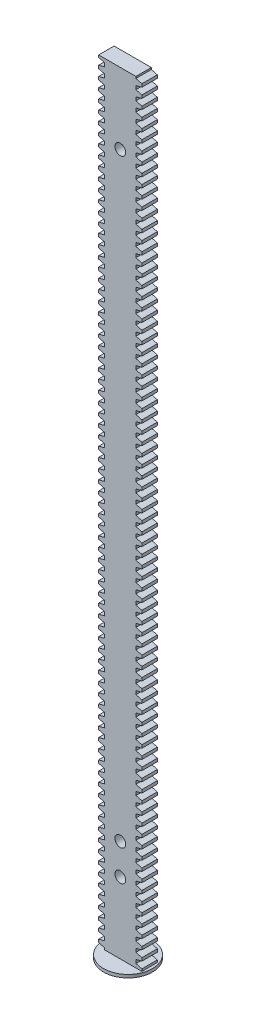
SolidWorks part; units mm, degrees
ref_plane "前视基准面" through (0, 0, 0) normal (0, 0, 1) x (1, 0, 0)
ref_plane "上视基准面" through (0, 0, 0) normal (0, 1, 0) x (1, 0, 0)
ref_plane "右视基准面" through (0, 0, 0) normal (1, 0, 0) x (0, 0, -1)
sketch "草图1" plane through (0, 0, 0) normal (0, 0, 1) x (1, 0, 0)
  line L0 (-85.9552, 233.5699) -> (-75.9552, 233.5699)
  line L1 (-86.008, 232.3319) -> (-86.008, 231.1796)
  line L2 (-86.008, 231.1796) -> (-87.9552, 230.676)
  line L3 (-87.9552, 230.676) -> (-87.9552, 229.6939)
  line L4 (-87.9552, 229.6939) -> (-86.008, 229.1903)
  line L5 (-86.008, 229.1903) -> (-86.008, 228.038)
  line L6 (-86.008, 228.038) -> (-87.9552, 227.5344)
  line L7 (-87.9552, 227.5344) -> (-87.9552, 226.5523)
  line L8 (-87.9552, 226.5523) -> (-86.008, 226.0487)
  line L9 (-86.008, 226.0487) -> (-86.008, 224.8964)
  line L10 (-86.008, 224.8964) -> (-87.9552, 224.3928)
  line L11 (-87.9552, 224.3928) -> (-87.9552, 223.4107)
  line L12 (-87.9552, 223.4107) -> (-86.008, 222.9071)
  line L13 (-86.008, 222.9071) -> (-86.008, 221.7548)
  line L14 (-86.008, 221.7548) -> (-87.9552, 221.2513)
  line L15 (-87.9552, 221.2513) -> (-87.9552, 220.2691)
  line L16 (-87.9552, 220.2691) -> (-86.008, 219.7655)
  line L17 (-86.008, 219.7655) -> (-86.008, 218.6132)
  line L18 (-86.008, 218.6132) -> (-87.9552, 218.1097)
  line L19 (-87.9552, 218.1097) -> (-87.9552, 217.1275)
  line L20 (-87.9552, 217.1275) -> (-86.008, 216.6239)
  line L21 (-86.008, 216.6239) -> (-86.008, 215.4717)
  line L22 (-86.008, 215.4717) -> (-87.9552, 214.9681)
  line L23 (-87.9552, 214.9681) -> (-87.9552, 213.9859)
  line L24 (-87.9552, 213.9859) -> (-86.008, 213.4823)
  line L25 (-86.008, 213.4823) -> (-86.008, 212.3301)
  line L26 (-86.008, 212.3301) -> (-87.9552, 211.8265)
  line L27 (-87.9552, 211.8265) -> (-87.9552, 210.8443)
  line L28 (-87.9552, 210.8443) -> (-86.008, 210.3407)
  line L29 (-86.008, 210.3407) -> (-86.008, 209.1885)
  line L30 (-86.008, 209.1885) -> (-87.9552, 208.6849)
  line L31 (-87.9552, 208.6849) -> (-87.9552, 207.7027)
  line L32 (-87.9552, 207.7027) -> (-86.008, 207.1991)
  line L33 (-86.008, 207.1991) -> (-86.008, 206.0469)
  line L34 (-86.008, 206.0469) -> (-87.9552, 205.5433)
  line L35 (-87.9552, 205.5433) -> (-87.9552, 204.5611)
  line L36 (-87.9552, 204.5611) -> (-86.008, 204.0575)
  line L37 (-86.008, 204.0575) -> (-86.008, 202.9053)
  line L38 (-86.008, 202.9053) -> (-87.9552, 202.4017)
  line L39 (-87.9552, 202.4017) -> (-87.9552, 201.4195)
  line L40 (-87.9552, 201.4195) -> (-86.008, 200.9159)
  line L41 (-86.008, 200.9159) -> (-86.008, 199.7637)
  line L42 (-86.008, 199.7637) -> (-87.9552, 199.2601)
  line L43 (-87.9552, 199.2601) -> (-87.9552, 198.2779)
  line L44 (-87.9552, 198.2779) -> (-86.008, 197.7743)
  line L45 (-86.008, 197.7743) -> (-86.008, 196.6221)
  line L46 (-86.008, 196.6221) -> (-87.9552, 196.1185)
  line L47 (-87.9552, 196.1185) -> (-87.9552, 195.1363)
  line L48 (-87.9552, 195.1363) -> (-86.008, 194.6328)
  line L49 (-86.008, 194.6328) -> (-86.008, 193.4805)
  line L50 (-86.008, 193.4805) -> (-87.9552, 192.9769)
  line L51 (-87.9552, 192.9769) -> (-87.9552, 191.9947)
  line L52 (-87.9552, 191.9947) -> (-86.008, 191.4912)
  line L53 (-86.008, 191.4912) -> (-86.008, 190.3389)
  line L54 (-86.008, 190.3389) -> (-87.9552, 189.8353)
  line L55 (-87.9552, 189.8353) -> (-87.9552, 188.8531)
  line L56 (-87.9552, 188.8531) -> (-86.008, 188.3496)
  line L57 (-86.008, 188.3496) -> (-86.008, 187.1973)
  line L58 (-86.008, 187.1973) -> (-87.9552, 186.6937)
  line L59 (-87.9552, 186.6937) -> (-87.9552, 185.7116)
  line L60 (-87.9552, 185.7116) -> (-86.008, 185.208)
  line L61 (-86.008, 185.208) -> (-86.008, 184.0557)
  line L62 (-86.008, 184.0557) -> (-87.9552, 183.5521)
  line L63 (-87.9552, 183.5521) -> (-87.9552, 182.57)
  line L64 (-87.9552, 182.57) -> (-86.008, 182.0664)
  line L65 (-86.008, 182.0664) -> (-86.008, 180.9141)
  line L66 (-86.008, 180.9141) -> (-87.9552, 180.4106)
  line L67 (-87.9552, 180.4106) -> (-87.9552, 179.4284)
  line L68 (-87.9552, 179.4284) -> (-86.008, 178.9248)
  line L69 (-86.008, 178.9248) -> (-86.008, 177.7725)
  line L70 (-86.008, 177.7725) -> (-87.9552, 177.269)
  line L71 (-87.9552, 177.269) -> (-87.9552, 176.2868)
  line L72 (-87.9552, 176.2868) -> (-86.008, 175.7832)
  line L73 (-86.008, 175.7832) -> (-86.008, 174.6309)
  line L74 (-86.008, 174.6309) -> (-87.9552, 174.1274)
  line L75 (-87.9552, 174.1274) -> (-87.9552, 173.1452)
  line L76 (-87.9552, 173.1452) -> (-86.008, 172.6416)
  line L77 (-86.008, 172.6416) -> (-86.008, 171.4894)
  line L78 (-86.008, 171.4894) -> (-87.9552, 170.9858)
  line L79 (-87.9552, 170.9858) -> (-87.9552, 170.0036)
  line L80 (-87.9552, 170.0036) -> (-86.008, 169.5)
  line L81 (-86.008, 169.5) -> (-86.008, 168.3478)
  line L82 (-86.008, 168.3478) -> (-87.9552, 167.8442)
  line L83 (-87.9552, 167.8442) -> (-87.9552, 166.862)
  line L84 (-87.9552, 166.862) -> (-86.008, 166.3584)
  line L85 (-86.008, 166.3584) -> (-86.008, 165.2062)
  line L86 (-86.008, 165.2062) -> (-87.9552, 164.7026)
  line L87 (-87.9552, 164.7026) -> (-87.9552, 163.7204)
  line L88 (-87.9552, 163.7204) -> (-86.008, 163.2168)
  line L89 (-86.008, 163.2168) -> (-86.008, 162.0646)
  line L90 (-86.008, 162.0646) -> (-87.9552, 161.561)
  line L91 (-87.9552, 161.561) -> (-87.9552, 160.5788)
  line L92 (-87.9552, 160.5788) -> (-86.008, 160.0752)
  line L93 (-86.008, 160.0752) -> (-86.008, 158.923)
  line L94 (-86.008, 158.923) -> (-87.9552, 158.4194)
  line L95 (-87.9552, 158.4194) -> (-87.9552, 157.4372)
  line L96 (-87.9552, 157.4372) -> (-86.008, 156.9336)
  line L97 (-86.008, 156.9336) -> (-86.008, 155.7814)
  line L98 (-86.008, 155.7814) -> (-87.9552, 155.2778)
  line L99 (-87.9552, 155.2778) -> (-87.9552, 154.2956)
  line L100 (-87.9552, 154.2956) -> (-86.008, 153.7921)
  line L101 (-86.008, 153.7921) -> (-86.008, 152.6398)
  line L102 (-86.008, 152.6398) -> (-87.9552, 152.1362)
  line L103 (-87.9552, 152.1362) -> (-87.9552, 151.154)
  line L104 (-87.9552, 151.154) -> (-86.008, 150.6505)
  line L105 (-86.008, 150.6505) -> (-86.008, 149.4982)
  line L106 (-86.008, 149.4982) -> (-87.9552, 148.9946)
  line L107 (-87.9552, 148.9946) -> (-87.9552, 148.0124)
  line L108 (-87.9552, 148.0124) -> (-86.008, 147.5089)
  line L109 (-86.008, 147.5089) -> (-86.008, 146.3566)
  line L110 (-86.008, 146.3566) -> (-87.9552, 145.853)
  line L111 (-87.9552, 145.853) -> (-87.9552, 144.8709)
  line L112 (-87.9552, 144.8709) -> (-86.008, 144.3673)
  line L113 (-86.008, 144.3673) -> (-86.008, 143.215)
  line L114 (-86.008, 143.215) -> (-87.9552, 142.7114)
  line L115 (-87.9552, 142.7114) -> (-87.9552, 141.7293)
  line L116 (-87.9552, 141.7293) -> (-86.008, 141.2257)
  line L117 (-86.008, 141.2257) -> (-86.008, 140.0734)
  line L118 (-86.008, 140.0734) -> (-87.9552, 139.5698)
  line L119 (-87.9552, 139.5698) -> (-87.9552, 138.5877)
  line L120 (-87.9552, 138.5877) -> (-86.008, 138.0841)
  line L121 (-86.008, 138.0841) -> (-86.008, 136.9318)
  line L122 (-86.008, 136.9318) -> (-87.9552, 136.4283)
  line L123 (-87.9552, 136.4283) -> (-87.9552, 135.4461)
  line L124 (-87.9552, 135.4461) -> (-86.008, 134.9425)
  line L125 (-86.008, 134.9425) -> (-86.008, 133.7902)
  line L126 (-86.008, 133.7902) -> (-87.9552, 133.2867)
  line L127 (-87.9552, 133.2867) -> (-87.9552, 132.3045)
  line L128 (-87.9552, 132.3045) -> (-86.008, 131.8009)
  line L129 (-86.008, 131.8009) -> (-86.008, 130.6486)
  line L130 (-86.008, 130.6486) -> (-87.9552, 130.1451)
  line L131 (-87.9552, 130.1451) -> (-87.9552, 129.1629)
  line L132 (-87.9552, 129.1629) -> (-86.008, 128.6593)
  line L133 (-86.008, 128.6593) -> (-86.008, 127.5071)
  line L134 (-86.008, 127.5071) -> (-87.9552, 127.0035)
  line L135 (-87.9552, 127.0035) -> (-87.9552, 126.0213)
  line L136 (-87.9552, 126.0213) -> (-86.008, 125.5177)
  line L137 (-86.008, 125.5177) -> (-86.008, 124.3655)
  line L138 (-86.008, 124.3655) -> (-87.9552, 123.8619)
  line L139 (-87.9552, 123.8619) -> (-87.9552, 122.8797)
  line L140 (-87.9552, 122.8797) -> (-86.008, 122.3761)
  line L141 (-86.008, 122.3761) -> (-86.008, 121.2239)
  line L142 (-86.008, 121.2239) -> (-87.9552, 120.7203)
  line L143 (-87.9552, 120.7203) -> (-87.9552, 119.7381)
  line L144 (-87.9552, 119.7381) -> (-86.008, 119.2345)
  line L145 (-86.008, 119.2345) -> (-86.008, 118.0823)
  line L146 (-86.008, 118.0823) -> (-87.9552, 117.5787)
  line L147 (-87.9552, 117.5787) -> (-87.9552, 116.5965)
  line L148 (-87.9552, 116.5965) -> (-86.008, 116.0929)
  line L149 (-86.008, 116.0929) -> (-86.008, 114.9407)
  line L150 (-86.008, 114.9407) -> (-87.9552, 114.4371)
  line L151 (-87.9552, 114.4371) -> (-87.9552, 113.4549)
  line L152 (-87.9552, 113.4549) -> (-86.008, 112.9513)
  line L153 (-86.008, 112.9513) -> (-86.008, 111.7991)
  line L154 (-86.008, 111.7991) -> (-87.9552, 111.2955)
  line L155 (-87.9552, 111.2955) -> (-87.9552, 110.3133)
  line L156 (-87.9552, 110.3133) -> (-86.008, 109.8098)
  line L157 (-86.008, 109.8098) -> (-86.008, 108.6575)
  line L158 (-86.008, 108.6575) -> (-87.9552, 108.1539)
  line L159 (-87.9552, 108.1539) -> (-87.9552, 107.1717)
  line L160 (-87.9552, 107.1717) -> (-86.008, 106.6682)
  line L161 (-86.008, 106.6682) -> (-86.008, 105.5159)
  line L162 (-86.008, 105.5159) -> (-87.9552, 105.0123)
  line L163 (-87.9552, 105.0123) -> (-87.9552, 104.0301)
  line L164 (-87.9552, 104.0301) -> (-86.008, 103.5266)
  line L165 (-86.008, 103.5266) -> (-86.008, 102.3743)
  line L166 (-86.008, 102.3743) -> (-87.9552, 101.8707)
  line L167 (-87.9552, 101.8707) -> (-87.9552, 100.8886)
  line L168 (-87.9552, 100.8886) -> (-86.008, 100.385)
  line L169 (-86.008, 100.385) -> (-86.008, 99.2327)
  line L170 (-86.008, 99.2327) -> (-87.9552, 98.7291)
  line L171 (-87.9552, 98.7291) -> (-87.9552, 97.747)
  line L172 (-87.9552, 97.747) -> (-86.008, 97.2434)
  line L173 (-86.008, 97.2434) -> (-86.008, 96.0911)
  line L174 (-86.008, 96.0911) -> (-87.9552, 95.5876)
  line L175 (-87.9552, 95.5876) -> (-87.9552, 94.6054)
  line L176 (-87.9552, 94.6054) -> (-86.008, 94.1018)
  line L177 (-86.008, 94.1018) -> (-86.008, 92.9495)
  line L178 (-86.008, 92.9495) -> (-87.9552, 92.446)
  line L179 (-87.9552, 92.446) -> (-87.9552, 91.4638)
  line L180 (-87.9552, 91.4638) -> (-86.008, 90.9602)
  line L181 (-86.008, 90.9602) -> (-86.008, 89.8079)
  line L182 (-86.008, 89.8079) -> (-87.9552, 89.3044)
  line L183 (-87.9552, 89.3044) -> (-87.9552, 88.3222)
  line L184 (-87.9552, 88.3222) -> (-86.008, 87.8186)
  line L185 (-86.008, 87.8186) -> (-86.008, 86.6664)
  line L186 (-86.008, 86.6664) -> (-87.9552, 86.1628)
  line L187 (-87.9552, 86.1628) -> (-87.9552, 85.1806)
  line L188 (-87.9552, 85.1806) -> (-86.008, 84.677)
  line L189 (-86.008, 84.677) -> (-86.008, 83.5248)
  line L190 (-86.008, 83.5248) -> (-87.9552, 83.0212)
  line L191 (-87.9552, 83.0212) -> (-87.9552, 82.039)
  line L192 (-87.9552, 82.039) -> (-86.008, 81.5354)
  line L193 (-86.008, 81.5354) -> (-86.008, 80.3832)
  line L194 (-86.008, 80.3832) -> (-87.9552, 79.8796)
  line L195 (-87.9552, 79.8796) -> (-87.9552, 78.8974)
  line L196 (-87.9552, 78.8974) -> (-86.008, 78.3938)
  line L197 (-86.008, 78.3938) -> (-86.008, 77.2416)
  line L198 (-86.008, 77.2416) -> (-87.9552, 76.738)
  line L199 (-87.9552, 76.738) -> (-87.9552, 75.7558)
  line L200 (-87.9552, 75.7558) -> (-86.008, 75.2522)
  line L201 (-86.008, 75.2522) -> (-86.008, 74.1)
  line L202 (-86.008, 74.1) -> (-87.9552, 73.5964)
  line L203 (-87.9552, 73.5964) -> (-87.9552, 72.6142)
  line L204 (-87.9552, 72.6142) -> (-86.008, 72.1106)
  line L205 (-86.008, 72.1106) -> (-86.008, 70.9584)
  line L206 (-86.008, 70.9584) -> (-87.9552, 70.4548)
  line L207 (-87.9552, 70.4548) -> (-87.9552, 69.4726)
  line L208 (-87.9552, 69.4726) -> (-86.008, 68.969)
  line L209 (-86.008, 68.969) -> (-86.008, 67.8168)
  line L210 (-86.008, 67.8168) -> (-87.9552, 67.3132)
  line L211 (-87.9552, 67.3132) -> (-87.9552, 66.331)
  line L212 (-87.9552, 66.331) -> (-86.008, 65.8275)
  line L213 (-86.008, 65.8275) -> (-86.008, 64.6752)
  line L214 (-86.008, 64.6752) -> (-87.9552, 64.1716)
  line L215 (-87.9552, 64.1716) -> (-87.9552, 63.1894)
  line L216 (-87.9552, 63.1894) -> (-86.008, 62.6859)
  line L217 (-86.008, 62.6859) -> (-86.008, 61.5336)
  line L218 (-86.008, 61.5336) -> (-87.9552, 61.03)
  line L219 (-87.9552, 61.03) -> (-87.9552, 60.0479)
  line L220 (-87.9552, 60.0479) -> (-86.008, 59.5443)
  line L221 (-86.008, 59.5443) -> (-86.008, 58.392)
  line L222 (-86.008, 58.392) -> (-87.9552, 57.8884)
  line L223 (-87.9552, 57.8884) -> (-87.9552, 56.9063)
  line L224 (-87.9552, 56.9063) -> (-86.008, 56.4027)
  line L225 (-86.008, 56.4027) -> (-86.008, 55.2504)
  line L226 (-86.008, 55.2504) -> (-87.9552, 54.7468)
  line L227 (-87.9552, 54.7468) -> (-87.9552, 53.7647)
  line L228 (-87.9552, 53.7647) -> (-86.008, 53.2611)
  line L229 (-86.008, 53.2611) -> (-86.008, 52.1088)
  line L230 (-86.008, 52.1088) -> (-87.9552, 51.6053)
  line L231 (-87.9552, 51.6053) -> (-87.9552, 50.6231)
  line L232 (-87.9552, 50.6231) -> (-86.008, 50.1195)
  line L233 (-86.008, 50.1195) -> (-86.008, 48.9672)
  line L234 (-86.008, 48.9672) -> (-87.9552, 48.4637)
  line L235 (-87.9552, 48.4637) -> (-87.9552, 47.4815)
  line L236 (-87.9552, 47.4815) -> (-86.008, 46.9779)
  line L237 (-86.008, 46.9779) -> (-86.008, 45.8256)
  line L238 (-86.008, 45.8256) -> (-87.9552, 45.3221)
  line L239 (-87.9552, 45.3221) -> (-87.9552, 44.3399)
  line L240 (-87.9552, 44.3399) -> (-86.008, 43.8363)
  line L241 (-86.008, 43.8363) -> (-86.008, 42.6841)
  line L242 (-86.008, 42.6841) -> (-87.9552, 42.1805)
  line L243 (-87.9552, 42.1805) -> (-87.9552, 41.1983)
  line L244 (-87.9552, 41.1983) -> (-86.008, 40.6947)
  line L245 (-86.008, 40.6947) -> (-86.008, 39.5425)
  line L246 (-86.008, 39.5425) -> (-87.9552, 39.0389)
  line L247 (-87.9552, 39.0389) -> (-87.9552, 38.0567)
  line L248 (-87.9552, 38.0567) -> (-86.008, 37.5531)
  line L249 (-86.008, 37.5531) -> (-86.008, 36.4009)
  line L250 (-86.008, 36.4009) -> (-87.9552, 35.8973)
  line L251 (-87.9552, 35.8973) -> (-87.9552, 34.9151)
  line L252 (-87.9552, 34.9151) -> (-86.008, 34.4115)
  line L253 (-86.008, 34.4115) -> (-86.008, 33.2593)
  line L254 (-86.008, 33.2593) -> (-87.9552, 32.7557)
  line L255 (-87.9552, 32.7557) -> (-87.9552, 31.7735)
  line L256 (-87.9552, 31.7735) -> (-86.008, 31.2699)
  line L257 (-86.008, 31.2699) -> (-86.008, 30.1177)
  line L258 (-86.008, 30.1177) -> (-87.9552, 29.6141)
  line L259 (-87.9552, 29.6141) -> (-87.9552, 28.6319)
  line L260 (-87.9552, 28.6319) -> (-86.008, 28.1283)
  line L261 (-86.008, 28.1283) -> (-86.008, 26.9761)
  line L262 (-86.008, 26.9761) -> (-87.9552, 26.4725)
  line L263 (-87.9552, 26.4725) -> (-87.9552, 25.4903)
  line L264 (-87.9552, 25.4903) -> (-86.008, 24.9868)
  line L265 (-86.008, 24.9868) -> (-86.008, 23.8345)
  line L266 (-86.008, 23.8345) -> (-87.9552, 23.3309)
  line L267 (-87.9552, 23.3309) -> (-87.9552, 22.3487)
  line L268 (-87.9552, 22.3487) -> (-86.008, 21.8452)
  line L269 (-86.008, 21.8452) -> (-86.008, 20.6929)
  line L270 (-86.008, 20.6929) -> (-87.9552, 20.1893)
  line L271 (-87.9552, 20.1893) -> (-87.9552, 19.2071)
  line L272 (-87.9552, 19.2071) -> (-86.008, 18.7036)
  line L273 (-86.008, 18.7036) -> (-86.008, 17.5513)
  line L274 (-86.008, 17.5513) -> (-87.9552, 17.0477)
  line L275 (-87.9552, 17.0477) -> (-87.9552, 16.0656)
  line L276 (-87.9552, 16.0656) -> (-86.008, 15.562)
  line L277 (-86.008, 15.562) -> (-86.008, 14.4097)
  line L278 (-86.008, 14.4097) -> (-87.9552, 13.9061)
  line L279 (-87.9552, 13.9061) -> (-87.9552, 12.924)
  line L280 (-87.9552, 12.924) -> (-86.008, 12.4204)
  line L281 (-86.008, 12.4204) -> (-86.008, 11.2681)
  line L282 (-86.008, 11.2681) -> (-87.9552, 10.7645)
  line L283 (-87.9552, 10.7645) -> (-87.9552, 9.7824)
  line L284 (-87.9552, 9.7824) -> (-86.008, 9.2788)
  line L285 (-86.008, 9.2788) -> (-86.008, 8.1265)
  line L286 (-86.008, 8.1265) -> (-87.9552, 7.623)
  line L287 (-87.9552, 7.623) -> (-87.9552, 6.6408)
  line L288 (-87.9552, 6.6408) -> (-86.008, 6.1372)
  line L289 (-86.008, 6.1372) -> (-86.008, 4.9849)
  line L290 (-86.008, 4.9849) -> (-87.9552, 4.4814)
  line L291 (-87.9552, 4.4814) -> (-87.9552, 3.4992)
  line L292 (-87.9552, 3.4992) -> (-86.008, 2.9956)
  line L293 (-86.008, 2.9956) -> (-86.008, 1.8434)
  line L294 (-86.008, 1.8434) -> (-87.9552, 1.3398)
  line L295 (-87.9552, 1.3398) -> (-87.9552, 0.3576)
  line L296 (-87.9552, 0.3576) -> (-86.008, -0.146)
  line L297 (-86.008, -0.146) -> (-86.008, -1.2982)
  line L298 (-86.008, -1.2982) -> (-87.9552, -1.8018)
  line L299 (-87.9552, -1.8018) -> (-87.9552, -2.784)
  line L300 (-87.9552, -2.784) -> (-86.008, -3.2876)
  line L301 (-86.008, -3.2876) -> (-86.008, -4.4398)
  line L302 (-86.008, -4.4398) -> (-87.9552, -4.9434)
  line L303 (-87.9552, -4.9434) -> (-87.9552, -5.9256)
  line L304 (-87.9552, -5.9256) -> (-86.008, -6.4292)
  line L305 (-86.008, -6.4292) -> (-86.008, -7.5814)
  line L306 (-86.008, -7.5814) -> (-87.9552, -8.085)
  line L307 (-87.9552, -8.085) -> (-87.9552, -9.0672)
  line L308 (-87.9552, -9.0672) -> (-86.008, -9.5708)
  line L309 (-86.008, -9.5708) -> (-86.008, -10.723)
  line L310 (-86.008, -10.723) -> (-87.9552, -11.2266)
  line L311 (-87.9552, -11.2266) -> (-87.9552, -12.2088)
  line L312 (-87.9552, -12.2088) -> (-86.008, -12.7124)
  line L313 (-86.008, -12.7124) -> (-86.008, -13.8646)
  line L314 (-86.008, -13.8646) -> (-87.9552, -14.3682)
  line L315 (-87.9552, -14.3682) -> (-87.9552, -15.3504)
  line L316 (-87.9552, -15.3504) -> (-86.008, -15.854)
  line L317 (-86.008, -15.854) -> (-86.008, -16.4301)
  line L318 (-86.008, -16.4301) -> (-85.9552, -16.4301) construction
  line L319 (-85.9552, -16.4301) -> (-85.9552, 233.5699) construction
  line L320 (-85.9552, 233.5699) -> (-87.9552, 233.5699)
  line L321 (-87.9552, 233.5699) -> (-87.9552, 232.8354)
  line L322 (-87.9552, 232.8354) -> (-86.008, 232.3319)
  line L323 (-75.9552, 233.5699) -> (-75.9552, -16.4301) construction
  line L324 (-75.9552, -16.4301) -> (-86.008, -16.4301)
  line L325 (-75.9024, -15.192) -> (-75.9024, -14.0398)
  line L326 (-75.9024, -14.0398) -> (-73.9552, -13.5362)
  line L327 (-73.9552, -13.5362) -> (-73.9552, -12.554)
  line L328 (-73.9552, -12.554) -> (-75.9024, -12.0504)
  line L329 (-75.9024, -12.0504) -> (-75.9024, -10.8982)
  line L330 (-75.9024, -10.8982) -> (-73.9552, -10.3946)
  line L331 (-73.9552, -10.3946) -> (-73.9552, -9.4124)
  line L332 (-73.9552, -9.4124) -> (-75.9024, -8.9088)
  line L333 (-75.9024, -8.9088) -> (-75.9024, -7.7566)
  line L334 (-75.9024, -7.7566) -> (-73.9552, -7.253)
  line L335 (-73.9552, -7.253) -> (-73.9552, -6.2708)
  line L336 (-73.9552, -6.2708) -> (-75.9024, -5.7672)
  line L337 (-75.9024, -5.7672) -> (-75.9024, -4.615)
  line L338 (-75.9024, -4.615) -> (-73.9552, -4.1114)
  line L339 (-73.9552, -4.1114) -> (-73.9552, -3.1292)
  line L340 (-73.9552, -3.1292) -> (-75.9024, -2.6257)
  line L341 (-75.9024, -2.6257) -> (-75.9024, -1.4734)
  line L342 (-75.9024, -1.4734) -> (-73.9552, -0.9698)
  line L343 (-73.9552, -0.9698) -> (-73.9552, 0.0124)
  line L344 (-73.9552, 0.0124) -> (-75.9024, 0.5159)
  line L345 (-75.9024, 0.5159) -> (-75.9024, 1.6682)
  line L346 (-75.9024, 1.6682) -> (-73.9552, 2.1718)
  line L347 (-73.9552, 2.1718) -> (-73.9552, 3.154)
  line L348 (-73.9552, 3.154) -> (-75.9024, 3.6575)
  line L349 (-75.9024, 3.6575) -> (-75.9024, 4.8098)
  line L350 (-75.9024, 4.8098) -> (-73.9552, 5.3134)
  line L351 (-73.9552, 5.3134) -> (-73.9552, 6.2955)
  line L352 (-73.9552, 6.2955) -> (-75.9024, 6.7991)
  line L353 (-75.9024, 6.7991) -> (-75.9024, 7.9514)
  line L354 (-75.9024, 7.9514) -> (-73.9552, 8.455)
  line L355 (-73.9552, 8.455) -> (-73.9552, 9.4371)
  line L356 (-73.9552, 9.4371) -> (-75.9024, 9.9407)
  line L357 (-75.9024, 9.9407) -> (-75.9024, 11.093)
  line L358 (-75.9024, 11.093) -> (-73.9552, 11.5965)
  line L359 (-73.9552, 11.5965) -> (-73.9552, 12.5787)
  line L360 (-73.9552, 12.5787) -> (-75.9024, 13.0823)
  line L361 (-75.9024, 13.0823) -> (-75.9024, 14.2346)
  line L362 (-75.9024, 14.2346) -> (-73.9552, 14.7381)
  line L363 (-73.9552, 14.7381) -> (-73.9552, 15.7203)
  line L364 (-73.9552, 15.7203) -> (-75.9024, 16.2239)
  line L365 (-75.9024, 16.2239) -> (-75.9024, 17.3762)
  line L366 (-75.9024, 17.3762) -> (-73.9552, 17.8797)
  line L367 (-73.9552, 17.8797) -> (-73.9552, 18.8619)
  line L368 (-73.9552, 18.8619) -> (-75.9024, 19.3655)
  line L369 (-75.9024, 19.3655) -> (-75.9024, 20.5177)
  line L370 (-75.9024, 20.5177) -> (-73.9552, 21.0213)
  line L371 (-73.9552, 21.0213) -> (-73.9552, 22.0035)
  line L372 (-73.9552, 22.0035) -> (-75.9024, 22.5071)
  line L373 (-75.9024, 22.5071) -> (-75.9024, 23.6593)
  line L374 (-75.9024, 23.6593) -> (-73.9552, 24.1629)
  line L375 (-73.9552, 24.1629) -> (-73.9552, 25.1451)
  line L376 (-73.9552, 25.1451) -> (-75.9024, 25.6487)
  line L377 (-75.9024, 25.6487) -> (-75.9024, 26.8009)
  line L378 (-75.9024, 26.8009) -> (-73.9552, 27.3045)
  line L379 (-73.9552, 27.3045) -> (-73.9552, 28.2867)
  line L380 (-73.9552, 28.2867) -> (-75.9024, 28.7903)
  line L381 (-75.9024, 28.7903) -> (-75.9024, 29.9425)
  line L382 (-75.9024, 29.9425) -> (-73.9552, 30.4461)
  line L383 (-73.9552, 30.4461) -> (-73.9552, 31.4283)
  line L384 (-73.9552, 31.4283) -> (-75.9024, 31.9319)
  line L385 (-75.9024, 31.9319) -> (-75.9024, 33.0841)
  line L386 (-75.9024, 33.0841) -> (-73.9552, 33.5877)
  line L387 (-73.9552, 33.5877) -> (-73.9552, 34.5699)
  line L388 (-73.9552, 34.5699) -> (-75.9024, 35.0735)
  line L389 (-75.9024, 35.0735) -> (-75.9024, 36.2257)
  line L390 (-75.9024, 36.2257) -> (-73.9552, 36.7293)
  line L391 (-73.9552, 36.7293) -> (-73.9552, 37.7115)
  line L392 (-73.9552, 37.7115) -> (-75.9024, 38.2151)
  line L393 (-75.9024, 38.2151) -> (-75.9024, 39.3673)
  line L394 (-75.9024, 39.3673) -> (-73.9552, 39.8709)
  line L395 (-73.9552, 39.8709) -> (-73.9552, 40.8531)
  line L396 (-73.9552, 40.8531) -> (-75.9024, 41.3566)
  line L397 (-75.9024, 41.3566) -> (-75.9024, 42.5089)
  line L398 (-75.9024, 42.5089) -> (-73.9552, 43.0125)
  line L399 (-73.9552, 43.0125) -> (-73.9552, 43.9947)
  line L400 (-73.9552, 43.9947) -> (-75.9024, 44.4982)
  line L401 (-75.9024, 44.4982) -> (-75.9024, 45.6505)
  line L402 (-75.9024, 45.6505) -> (-73.9552, 46.1541)
  line L403 (-73.9552, 46.1541) -> (-73.9552, 47.1362)
  line L404 (-73.9552, 47.1362) -> (-75.9024, 47.6398)
  line L405 (-75.9024, 47.6398) -> (-75.9024, 48.7921)
  line L406 (-75.9024, 48.7921) -> (-73.9552, 49.2957)
  line L407 (-73.9552, 49.2957) -> (-73.9552, 50.2778)
  line L408 (-73.9552, 50.2778) -> (-75.9024, 50.7814)
  line L409 (-75.9024, 50.7814) -> (-75.9024, 51.9337)
  line L410 (-75.9024, 51.9337) -> (-73.9552, 52.4373)
  line L411 (-73.9552, 52.4373) -> (-73.9552, 53.4194)
  line L412 (-73.9552, 53.4194) -> (-75.9024, 53.923)
  line L413 (-75.9024, 53.923) -> (-75.9024, 55.0753)
  line L414 (-75.9024, 55.0753) -> (-73.9552, 55.5788)
  line L415 (-73.9552, 55.5788) -> (-73.9552, 56.561)
  line L416 (-73.9552, 56.561) -> (-75.9024, 57.0646)
  line L417 (-75.9024, 57.0646) -> (-75.9024, 58.2169)
  line L418 (-75.9024, 58.2169) -> (-73.9552, 58.7204)
  line L419 (-73.9552, 58.7204) -> (-73.9552, 59.7026)
  line L420 (-73.9552, 59.7026) -> (-75.9024, 60.2062)
  line L421 (-75.9024, 60.2062) -> (-75.9024, 61.3585)
  line L422 (-75.9024, 61.3585) -> (-73.9552, 61.862)
  line L423 (-73.9552, 61.862) -> (-73.9552, 62.8442)
  line L424 (-73.9552, 62.8442) -> (-75.9024, 63.3478)
  line L425 (-75.9024, 63.3478) -> (-75.9024, 64.5)
  line L426 (-75.9024, 64.5) -> (-73.9552, 65.0036)
  line L427 (-73.9552, 65.0036) -> (-73.9552, 65.9858)
  line L428 (-73.9552, 65.9858) -> (-75.9024, 66.4894)
  line L429 (-75.9024, 66.4894) -> (-75.9024, 67.6416)
  line L430 (-75.9024, 67.6416) -> (-73.9552, 68.1452)
  line L431 (-73.9552, 68.1452) -> (-73.9552, 69.1274)
  line L432 (-73.9552, 69.1274) -> (-75.9024, 69.631)
  line L433 (-75.9024, 69.631) -> (-75.9024, 70.7832)
  line L434 (-75.9024, 70.7832) -> (-73.9552, 71.2868)
  line L435 (-73.9552, 71.2868) -> (-73.9552, 72.269)
  line L436 (-73.9552, 72.269) -> (-75.9024, 72.7726)
  line L437 (-75.9024, 72.7726) -> (-75.9024, 73.9248)
  line L438 (-75.9024, 73.9248) -> (-73.9552, 74.4284)
  line L439 (-73.9552, 74.4284) -> (-73.9552, 75.4106)
  line L440 (-73.9552, 75.4106) -> (-75.9024, 75.9142)
  line L441 (-75.9024, 75.9142) -> (-75.9024, 77.0664)
  line L442 (-75.9024, 77.0664) -> (-73.9552, 77.57)
  line L443 (-73.9552, 77.57) -> (-73.9552, 78.5522)
  line L444 (-73.9552, 78.5522) -> (-75.9024, 79.0558)
  line L445 (-75.9024, 79.0558) -> (-75.9024, 80.208)
  line L446 (-75.9024, 80.208) -> (-73.9552, 80.7116)
  line L447 (-73.9552, 80.7116) -> (-73.9552, 81.6938)
  line L448 (-73.9552, 81.6938) -> (-75.9024, 82.1973)
  line L449 (-75.9024, 82.1973) -> (-75.9024, 83.3496)
  line L450 (-75.9024, 83.3496) -> (-73.9552, 83.8532)
  line L451 (-73.9552, 83.8532) -> (-73.9552, 84.8354)
  line L452 (-73.9552, 84.8354) -> (-75.9024, 85.3389)
  line L453 (-75.9024, 85.3389) -> (-75.9024, 86.4912)
  line L454 (-75.9024, 86.4912) -> (-73.9552, 86.9948)
  line L455 (-73.9552, 86.9948) -> (-73.9552, 87.977)
  line L456 (-73.9552, 87.977) -> (-75.9024, 88.4805)
  line L457 (-75.9024, 88.4805) -> (-75.9024, 89.6328)
  line L458 (-75.9024, 89.6328) -> (-73.9552, 90.1364)
  line L459 (-73.9552, 90.1364) -> (-73.9552, 91.1185)
  line L460 (-73.9552, 91.1185) -> (-75.9024, 91.6221)
  line L461 (-75.9024, 91.6221) -> (-75.9024, 92.7744)
  line L462 (-75.9024, 92.7744) -> (-73.9552, 93.278)
  line L463 (-73.9552, 93.278) -> (-73.9552, 94.2601)
  line L464 (-73.9552, 94.2601) -> (-75.9024, 94.7637)
  line L465 (-75.9024, 94.7637) -> (-75.9024, 95.916)
  line L466 (-75.9024, 95.916) -> (-73.9552, 96.4196)
  line L467 (-73.9552, 96.4196) -> (-73.9552, 97.4017)
  line L468 (-73.9552, 97.4017) -> (-75.9024, 97.9053)
  line L469 (-75.9024, 97.9053) -> (-75.9024, 99.0576)
  line L470 (-75.9024, 99.0576) -> (-73.9552, 99.5611)
  line L471 (-73.9552, 99.5611) -> (-73.9552, 100.5433)
  line L472 (-73.9552, 100.5433) -> (-75.9024, 101.0469)
  line L473 (-75.9024, 101.0469) -> (-75.9024, 102.1992)
  line L474 (-75.9024, 102.1992) -> (-73.9552, 102.7027)
  line L475 (-73.9552, 102.7027) -> (-73.9552, 103.6849)
  line L476 (-73.9552, 103.6849) -> (-75.9024, 104.1885)
  line L477 (-75.9024, 104.1885) -> (-75.9024, 105.3407)
  line L478 (-75.9024, 105.3407) -> (-73.9552, 105.8443)
  line L479 (-73.9552, 105.8443) -> (-73.9552, 106.8265)
  line L480 (-73.9552, 106.8265) -> (-75.9024, 107.3301)
  line L481 (-75.9024, 107.3301) -> (-75.9024, 108.4823)
  line L482 (-75.9024, 108.4823) -> (-73.9552, 108.9859)
  line L483 (-73.9552, 108.9859) -> (-73.9552, 109.9681)
  line L484 (-73.9552, 109.9681) -> (-75.9024, 110.4717)
  line L485 (-75.9024, 110.4717) -> (-75.9024, 111.6239)
  line L486 (-75.9024, 111.6239) -> (-73.9552, 112.1275)
  line L487 (-73.9552, 112.1275) -> (-73.9552, 113.1097)
  line L488 (-73.9552, 113.1097) -> (-75.9024, 113.6133)
  line L489 (-75.9024, 113.6133) -> (-75.9024, 114.7655)
  line L490 (-75.9024, 114.7655) -> (-73.9552, 115.2691)
  line L491 (-73.9552, 115.2691) -> (-73.9552, 116.2513)
  line L492 (-73.9552, 116.2513) -> (-75.9024, 116.7549)
  line L493 (-75.9024, 116.7549) -> (-75.9024, 117.9071)
  line L494 (-75.9024, 117.9071) -> (-73.9552, 118.4107)
  line L495 (-73.9552, 118.4107) -> (-73.9552, 119.3929)
  line L496 (-73.9552, 119.3929) -> (-75.9024, 119.8965)
  line L497 (-75.9024, 119.8965) -> (-75.9024, 121.0487)
  line L498 (-75.9024, 121.0487) -> (-73.9552, 121.5523)
  line L499 (-73.9552, 121.5523) -> (-73.9552, 122.5345)
  line L500 (-73.9552, 122.5345) -> (-75.9024, 123.0381)
  line L501 (-75.9024, 123.0381) -> (-75.9024, 124.1903)
  line L502 (-75.9024, 124.1903) -> (-73.9552, 124.6939)
  line L503 (-73.9552, 124.6939) -> (-73.9552, 125.6761)
  line L504 (-73.9552, 125.6761) -> (-75.9024, 126.1796)
  line L505 (-75.9024, 126.1796) -> (-75.9024, 127.3319)
  line L506 (-75.9024, 127.3319) -> (-73.9552, 127.8355)
  line L507 (-73.9552, 127.8355) -> (-73.9552, 128.8177)
  line L508 (-73.9552, 128.8177) -> (-75.9024, 129.3212)
  line L509 (-75.9024, 129.3212) -> (-75.9024, 130.4735)
  line L510 (-75.9024, 130.4735) -> (-73.9552, 130.9771)
  line L511 (-73.9552, 130.9771) -> (-73.9552, 131.9593)
  line L512 (-73.9552, 131.9593) -> (-75.9024, 132.4628)
  line L513 (-75.9024, 132.4628) -> (-75.9024, 133.6151)
  line L514 (-75.9024, 133.6151) -> (-73.9552, 134.1187)
  line L515 (-73.9552, 134.1187) -> (-73.9552, 135.1008)
  line L516 (-73.9552, 135.1008) -> (-75.9024, 135.6044)
  line L517 (-75.9024, 135.6044) -> (-75.9024, 136.7567)
  line L518 (-75.9024, 136.7567) -> (-73.9552, 137.2603)
  line L519 (-73.9552, 137.2603) -> (-73.9552, 138.2424)
  line L520 (-73.9552, 138.2424) -> (-75.9024, 138.746)
  line L521 (-75.9024, 138.746) -> (-75.9024, 139.8983)
  line L522 (-75.9024, 139.8983) -> (-73.9552, 140.4018)
  line L523 (-73.9552, 140.4018) -> (-73.9552, 141.384)
  line L524 (-73.9552, 141.384) -> (-75.9024, 141.8876)
  line L525 (-75.9024, 141.8876) -> (-75.9024, 143.0399)
  line L526 (-75.9024, 143.0399) -> (-73.9552, 143.5434)
  line L527 (-73.9552, 143.5434) -> (-73.9552, 144.5256)
  line L528 (-73.9552, 144.5256) -> (-75.9024, 145.0292)
  line L529 (-75.9024, 145.0292) -> (-75.9024, 146.1815)
  line L530 (-75.9024, 146.1815) -> (-73.9552, 146.685)
  line L531 (-73.9552, 146.685) -> (-73.9552, 147.6672)
  line L532 (-73.9552, 147.6672) -> (-75.9024, 148.1708)
  line L533 (-75.9024, 148.1708) -> (-75.9024, 149.323)
  line L534 (-75.9024, 149.323) -> (-73.9552, 149.8266)
  line L535 (-73.9552, 149.8266) -> (-73.9552, 150.8088)
  line L536 (-73.9552, 150.8088) -> (-75.9024, 151.3124)
  line L537 (-75.9024, 151.3124) -> (-75.9024, 152.4646)
  line L538 (-75.9024, 152.4646) -> (-73.9552, 152.9682)
  line L539 (-73.9552, 152.9682) -> (-73.9552, 153.9504)
  line L540 (-73.9552, 153.9504) -> (-75.9024, 154.454)
  line L541 (-75.9024, 154.454) -> (-75.9024, 155.6062)
  line L542 (-75.9024, 155.6062) -> (-73.9552, 156.1098)
  line L543 (-73.9552, 156.1098) -> (-73.9552, 157.092)
  line L544 (-73.9552, 157.092) -> (-75.9024, 157.5956)
  line L545 (-75.9024, 157.5956) -> (-75.9024, 158.7478)
  line L546 (-75.9024, 158.7478) -> (-73.9552, 159.2514)
  line L547 (-73.9552, 159.2514) -> (-73.9552, 160.2336)
  line L548 (-73.9552, 160.2336) -> (-75.9024, 160.7372)
  line L549 (-75.9024, 160.7372) -> (-75.9024, 161.8894)
  line L550 (-75.9024, 161.8894) -> (-73.9552, 162.393)
  line L551 (-73.9552, 162.393) -> (-73.9552, 163.3752)
  line L552 (-73.9552, 163.3752) -> (-75.9024, 163.8788)
  line L553 (-75.9024, 163.8788) -> (-75.9024, 165.031)
  line L554 (-75.9024, 165.031) -> (-73.9552, 165.5346)
  line L555 (-73.9552, 165.5346) -> (-73.9552, 166.5168)
  line L556 (-73.9552, 166.5168) -> (-75.9024, 167.0203)
  line L557 (-75.9024, 167.0203) -> (-75.9024, 168.1726)
  line L558 (-75.9024, 168.1726) -> (-73.9552, 168.6762)
  line L559 (-73.9552, 168.6762) -> (-73.9552, 169.6584)
  line L560 (-73.9552, 169.6584) -> (-75.9024, 170.1619)
  line L561 (-75.9024, 170.1619) -> (-75.9024, 171.3142)
  line L562 (-75.9024, 171.3142) -> (-73.9552, 171.8178)
  line L563 (-73.9552, 171.8178) -> (-73.9552, 172.8)
  line L564 (-73.9552, 172.8) -> (-75.9024, 173.3035)
  line L565 (-75.9024, 173.3035) -> (-75.9024, 174.4558)
  line L566 (-75.9024, 174.4558) -> (-73.9552, 174.9594)
  line L567 (-73.9552, 174.9594) -> (-73.9552, 175.9415)
  line L568 (-73.9552, 175.9415) -> (-75.9024, 176.4451)
  line L569 (-75.9024, 176.4451) -> (-75.9024, 177.5974)
  line L570 (-75.9024, 177.5974) -> (-73.9552, 178.101)
  line L571 (-73.9552, 178.101) -> (-73.9552, 179.0831)
  line L572 (-73.9552, 179.0831) -> (-75.9024, 179.5867)
  line L573 (-75.9024, 179.5867) -> (-75.9024, 180.739)
  line L574 (-75.9024, 180.739) -> (-73.9552, 181.2426)
  line L575 (-73.9552, 181.2426) -> (-73.9552, 182.2247)
  line L576 (-73.9552, 182.2247) -> (-75.9024, 182.7283)
  line L577 (-75.9024, 182.7283) -> (-75.9024, 183.8806)
  line L578 (-75.9024, 183.8806) -> (-73.9552, 184.3841)
  line L579 (-73.9552, 184.3841) -> (-73.9552, 185.3663)
  line L580 (-73.9552, 185.3663) -> (-75.9024, 185.8699)
  line L581 (-75.9024, 185.8699) -> (-75.9024, 187.0222)
  line L582 (-75.9024, 187.0222) -> (-73.9552, 187.5257)
  line L583 (-73.9552, 187.5257) -> (-73.9552, 188.5079)
  line L584 (-73.9552, 188.5079) -> (-75.9024, 189.0115)
  line L585 (-75.9024, 189.0115) -> (-75.9024, 190.1638)
  line L586 (-75.9024, 190.1638) -> (-73.9552, 190.6673)
  line L587 (-73.9552, 190.6673) -> (-73.9552, 191.6495)
  line L588 (-73.9552, 191.6495) -> (-75.9024, 192.1531)
  line L589 (-75.9024, 192.1531) -> (-75.9024, 193.3053)
  line L590 (-75.9024, 193.3053) -> (-73.9552, 193.8089)
  line L591 (-73.9552, 193.8089) -> (-73.9552, 194.7911)
  line L592 (-73.9552, 194.7911) -> (-75.9024, 195.2947)
  line L593 (-75.9024, 195.2947) -> (-75.9024, 196.4469)
  line L594 (-75.9024, 196.4469) -> (-73.9552, 196.9505)
  line L595 (-73.9552, 196.9505) -> (-73.9552, 197.9327)
  line L596 (-73.9552, 197.9327) -> (-75.9024, 198.4363)
  line L597 (-75.9024, 198.4363) -> (-75.9024, 199.5885)
  line L598 (-75.9024, 199.5885) -> (-73.9552, 200.0921)
  line L599 (-73.9552, 200.0921) -> (-73.9552, 201.0743)
  line L600 (-73.9552, 201.0743) -> (-75.9024, 201.5779)
  line L601 (-75.9024, 201.5779) -> (-75.9024, 202.7301)
  line L602 (-75.9024, 202.7301) -> (-73.9552, 203.2337)
  line L603 (-73.9552, 203.2337) -> (-73.9552, 204.2159)
  line L604 (-73.9552, 204.2159) -> (-75.9024, 204.7195)
  line L605 (-75.9024, 204.7195) -> (-75.9024, 205.8717)
  line L606 (-75.9024, 205.8717) -> (-73.9552, 206.3753)
  line L607 (-73.9552, 206.3753) -> (-73.9552, 207.3575)
  line L608 (-73.9552, 207.3575) -> (-75.9024, 207.8611)
  line L609 (-75.9024, 207.8611) -> (-75.9024, 209.0133)
  line L610 (-75.9024, 209.0133) -> (-73.9552, 209.5169)
  line L611 (-73.9552, 209.5169) -> (-73.9552, 210.4991)
  line L612 (-73.9552, 210.4991) -> (-75.9024, 211.0026)
  line L613 (-75.9024, 211.0026) -> (-75.9024, 212.1549)
  line L614 (-75.9024, 212.1549) -> (-73.9552, 212.6585)
  line L615 (-73.9552, 212.6585) -> (-73.9552, 213.6407)
  line L616 (-73.9552, 213.6407) -> (-75.9024, 214.1442)
  line L617 (-75.9024, 214.1442) -> (-75.9024, 215.2965)
  line L618 (-75.9024, 215.2965) -> (-73.9552, 215.8001)
  line L619 (-73.9552, 215.8001) -> (-73.9552, 216.7823)
  line L620 (-73.9552, 216.7823) -> (-75.9024, 217.2858)
  line L621 (-75.9024, 217.2858) -> (-75.9024, 218.4381)
  line L622 (-75.9024, 218.4381) -> (-73.9552, 218.9417)
  line L623 (-73.9552, 218.9417) -> (-73.9552, 219.9238)
  line L624 (-73.9552, 219.9238) -> (-75.9024, 220.4274)
  line L625 (-75.9024, 220.4274) -> (-75.9024, 221.5797)
  line L626 (-75.9024, 221.5797) -> (-73.9552, 222.0833)
  line L627 (-73.9552, 222.0833) -> (-73.9552, 223.0654)
  line L628 (-73.9552, 223.0654) -> (-75.9024, 223.569)
  line L629 (-75.9024, 223.569) -> (-75.9024, 224.7213)
  line L630 (-75.9024, 224.7213) -> (-73.9552, 225.2248)
  line L631 (-73.9552, 225.2248) -> (-73.9552, 226.207)
  line L632 (-73.9552, 226.207) -> (-75.9024, 226.7106)
  line L633 (-75.9024, 226.7106) -> (-75.9024, 227.8629)
  line L634 (-75.9024, 227.8629) -> (-73.9552, 228.3664)
  line L635 (-73.9552, 228.3664) -> (-73.9552, 229.3486)
  line L636 (-73.9552, 229.3486) -> (-75.9024, 229.8522)
  line L637 (-75.9024, 229.8522) -> (-75.9024, 231.0045)
  line L638 (-75.9024, 231.0045) -> (-73.9552, 231.508)
  line L639 (-73.9552, 231.508) -> (-73.9552, 232.4902)
  line L640 (-73.9552, 232.4902) -> (-75.9024, 232.9938)
  line L641 (-75.9024, 232.9938) -> (-75.9024, 233.5699)
  line L642 (-75.9024, 233.5699) -> (-75.9552, 233.5699)
  line L643 (-75.9552, 233.5699) -> (-75.9552, -16.4301) construction
  line L644 (-73.9552, -15.6956) -> (-73.9552, -16.4301)
  line L645 (-73.9552, -16.4301) -> (-75.9552, -16.4301)
  line L646 (-73.9552, -15.6956) -> (-75.9024, -15.192)
  dimension "D1" = 2
  dimension "D2" = 10
extrude "凸台-拉伸1" add sketch "草图1" along normal blind 5
sketch "草图2" plane through (0, 0, 5) normal (0, 0, 1) x (1, 0, 0)
  line L0 (-75.9024, -12.0504) -> (-86.008, -12.0504) construction
  line L1 (-80.9552, -12.0504) -> (-80.9552, 3.5366) construction
  line L2 (-86.008, -16.4301) -> (-73.9552, -16.4301) construction
  line L3 (-86.008, 231.1796) -> (-75.9024, 231.1796) construction
  line L4 (-80.9552, 231.1796) -> (-80.9552, 226.0461) construction
  line L5 (-75.9024, 233.5699) -> (-87.9552, 233.5699) construction
  circle A0 centre (-80.9552, 6.5699) radius 1.75
  circle A1 centre (-80.9552, 16.5699) radius 1.75
  circle A2 centre (-80.9552, 210.5699) radius 1.75
  dimension "D1" = 3.5
  dimension "D3" = 3.5
  dimension "D5" = 3.5
  dimension "D2" = 23
  dimension "D4" = 10
  dimension "D6" = 23
extrude "切除-拉伸1" cut sketch "草图2" against normal blind 5
sketch "草图4" plane through (0, -16.4301, 0) normal (0, -1, 0) x (1, 0, 0)
  line L0 (-87.9552, 2.5) -> (-73.9552, 2.5) construction
  line L1 (-87.9552, 5) -> (-87.9552, 0) construction
  line L2 (-73.9552, 5) -> (-73.9552, 0) construction
  circle A0 centre (-80.9552, 2.5) radius 7.905
  dimension "D1" = 15.81
extrude "凸台-拉伸3" add sketch "草图4" along normal blind 1
